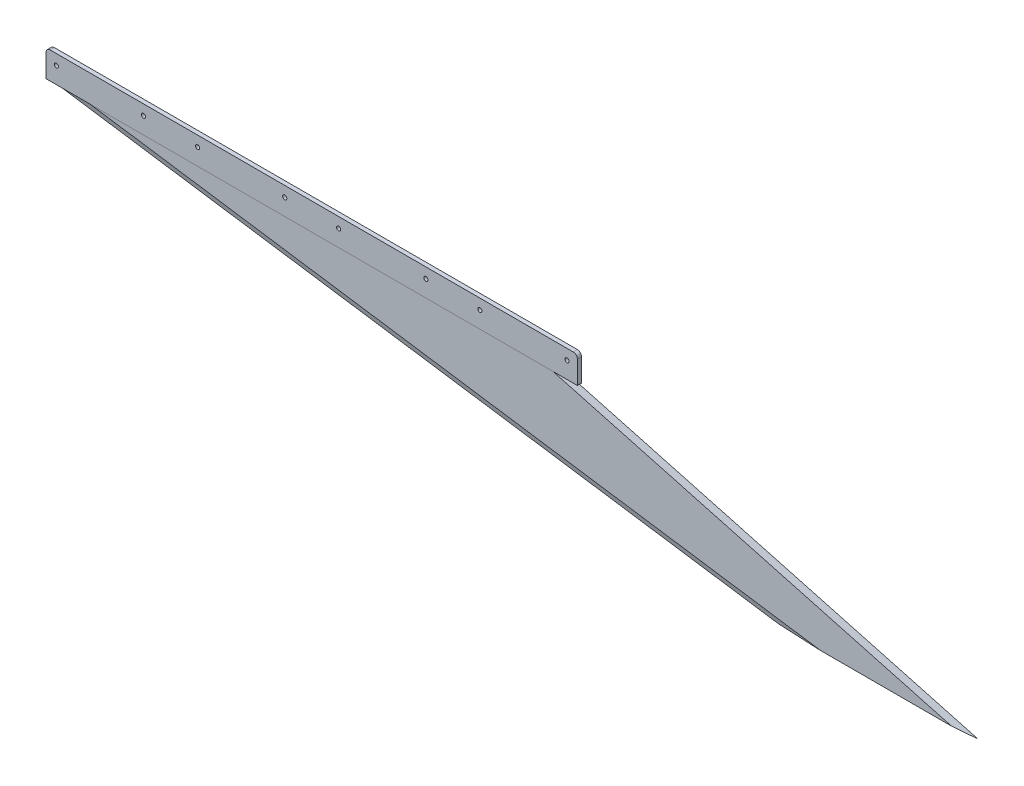
SolidWorks part; units mm, degrees
material "AS4"
ref_plane "Front Plane" through (0, 0, 0) normal (0, 0, 1) x (1, 0, 0)
ref_plane "Top Plane" through (0, 0, 0) normal (0, 1, 0) x (1, 0, 0)
ref_plane "Right Plane" through (0, 0, 0) normal (1, 0, 0) x (0, 0, -1)
sketch "Sketch1" plane through (0, 0, 0) normal (0, 0, 1) x (1, 0, 0)
  line L0 (-812.8, 0) -> (0, 0)
  line L2 (-812.8, 0) -> (304.8, -165.1)
  line L3 (304.8, -165.1) -> (609.6, -165.1)
  line L4 (609.6, -165.1) -> (0, 0)
  dimension "D1" = 812.8
  dimension "D3" = 1117.6
  dimension "D4" = 304.8
  dimension "D2" = 165.1
extrude "Boss-Extrude1" add sketch "Sketch1" along normal blind 6.35 contours L0 L4 L3 L2
ref_plane "Plane5" through (-795.4408, 117.5083, 0) normal (-0.9893, 0.1461, 0) x (0, 0, -1)
sketch "Sketch17" plane through (-795.4408, 117.5083, 0) normal (-0.9893, 0.1461, 0) x (0, 0, -1)
  line L0 (-3.175, 118.7836) -> (-3.175, 201.3214) construction
  line L1 (-6.35, 118.7836) -> (0, 118.7836) construction
  line L2 (-3.175, 118.7836) -> (-6.35, 109.0119)
  line L3 (-6.35, 118.7836) -> (-6.35, 0) construction
  line L4 (-3.175, 118.7836) -> (0, 109.0119)
  line L5 (0, 118.7836) -> (0, 74.2397) construction
  line L6 (-6.35, 109.0119) -> (-6.35, 209.9925)
  line L7 (0, 109.0119) -> (0, 209.9925)
  line L8 (-6.35, 209.9925) -> (0, 209.9925)
  dimension "D1" = 72
  dimension "D2" = 72
extrude "Cut-Extrude5" cut sketch "Sketch17" against normal through all
ref_plane "Plane2" through (609.6, -165.1, 0) normal (0.9652, -0.2614, 0) x (0, 0, -1)
sketch "Sketch18" plane through (609.6, -165.1, 0) normal (0.9652, -0.2614, 0) x (0, 0, -1)
  line L0 (-3.175, 0) -> (-3.175, -4.2063) construction
  line L2 (-6.35, 0) -> (0, 0) construction
  line L3 (-3.175, 0) -> (-6.35, -9.7716)
  line L4 (-6.35, -62.2) -> (-6.35, 0) construction
  line L5 (-3.175, 0) -> (0, -9.7716)
  line L6 (0, -212.4785) -> (0, 0) construction
  line L7 (-6.35, -9.7716) -> (-6.35, 0.8829)
  line L8 (0, -9.7716) -> (0, 0.8829)
  line L9 (-6.35, 0.8829) -> (0, 0.8829)
  dimension "D1" = 72
  dimension "D2" = 72
extrude "Cut-Extrude6" cut sketch "Sketch18" against normal blind 721.614
sketch "Sketch19" plane through (0, 0, 0) normal (0, 1, 0) x (1, 0, 0)
  line L0 (-812.8, 0) -> (304.8, 0) construction
  line L1 (-812.8, 0) -> (0, 0)
  line L2 (-812.8, 0) -> (-812.8, -6.35)
  line L3 (-812.8, -6.35) -> (0, -6.35)
  line L4 (0, 0) -> (0, -6.35)
  line L5 (-745.9356, -6.35) -> (-37.3798, -6.35) construction
  dimension "D1" = 812.8
extrude "Boss-Extrude8" add sketch "Sketch19" along normal blind 3.175
sketch "Sketch20" plane through (0, 3.175, 0) normal (0, 1, 0) x (1, 0, 0)
  line L0 (-812.8, -6.35) -> (0, -6.35) construction
  line L1 (-812.8, 0) -> (0, 0)
  line L2 (-812.8, 0) -> (-812.8, -6.35)
  line L3 (-812.8, -6.35) -> (0, -6.35)
  line L4 (0, 0) -> (0, -6.35)
  dimension "D1" = 812.8
extrude "Boss-Extrude9" add sketch "Sketch20" along normal blind 38.1
sketch "Sketch22" plane through (0, 0, 0) normal (0, 0, -1) x (-1, 0, 0)
  line L2 (812.8, 41.275) -> (812.8, 0) construction
  line L3 (812.8, 41.275) -> (0, 41.275) construction
  line L4 (663.575, 25.4) -> (149.225, 25.4) construction
  line L5 (406.4, 41.275) -> (406.4, 0) construction
  circle A1 centre (149.225, 25.4) radius 3.175
  circle A8 centre (796.925, 25.4) radius 3.175
  circle A9 centre (663.575, 25.4) radius 3.175
  circle A10 centre (581.025, 25.4) radius 3.175
  circle A11 centre (447.675, 25.4) radius 3.175
  circle A12 centre (365.125, 25.4) radius 3.175
  circle A13 centre (231.775, 25.4) radius 3.175
  circle A14 centre (149.225, 25.4) radius 3.175
  circle A15 centre (15.875, 25.4) radius 3.175
  dimension "D5" = 6.35
  dimension "D7" = 15.875
  dimension "D8" = 6.35
  dimension "D10" = 15.875
  dimension "D11" = 6.35
  dimension "D12" = 15.875
  dimension "D14" = 6.35
  dimension "D16" = 15.875
  dimension "D6" = 15.875
  dimension "D9" = 133.35
  dimension "D13" = 82.55
  dimension "D15" = 133.35
fillet "Fillet1" radius 6.35 1 edges at (0, 41.275, 3.175)
fillet "Fillet2" radius 6.35 1 edges at (-812.8, 41.275, 3.175)
extrude "Cut-Extrude7" cut sketch "Sketch22" against normal up to next contours A8 | A9 | A1 | A15 | A10 | A11 | A12 | A13
sketch "Sketch23" plane through (0, 0, 6.35) normal (0, 0, 1) x (1, 0, 0)
  line L1 (-37.3798, 0) -> (572.2202, -165.1) construction
  line L2 (371.6644, -165.1) -> (-745.9356, 0) construction
  line L3 (371.6644, -165.1) -> (572.2202, -165.1) construction
  line L4 (-37.3798, 0) -> (572.2202, -165.1)
  line L5 (371.6644, -165.1) -> (-745.9356, 0)
  line L6 (371.6644, -165.1) -> (572.2202, -165.1)
  line L7 (-745.9356, 0) -> (-37.3798, 0)
split line "Split Line3"
sketch "Sketch24" plane through (0, 0, 0) normal (0, 0, -1) x (-1, 0, 0)
  line L0 (-371.6644, -165.1) -> (-572.2202, -165.1) construction
  line L1 (37.3798, 0) -> (-572.2202, -165.1) construction
  line L2 (-371.6644, -165.1) -> (745.9356, 0) construction
  line L3 (-371.6644, -165.1) -> (-572.2202, -165.1)
  line L4 (37.3798, 0) -> (-572.2202, -165.1)
  line L5 (-371.6644, -165.1) -> (745.9356, 0)
  line L6 (37.3798, 0) -> (745.9356, 0)
split line "Split Line5"
equation "\"Fin Root Chord\"= 32in"
equation "\"Fin Thickness\"= 0.25in"
equation "\"Airframe Thickness\"= 0.125in"
equation "\"Bolt Diameter\"= 0.25in"
equation "\"D1@Sketch20\"=\"Fin Root Chord\""
equation "\"D1@Sketch1\"=\"Fin Root Chord\""
equation "\"D1@Boss-Extrude1\"=\"Fin Thickness\""
equation "\"D1@Sketch19\"=\"Fin Root Chord\""
equation "\"D1@Boss-Extrude8\"=\"Airframe Thickness\""
